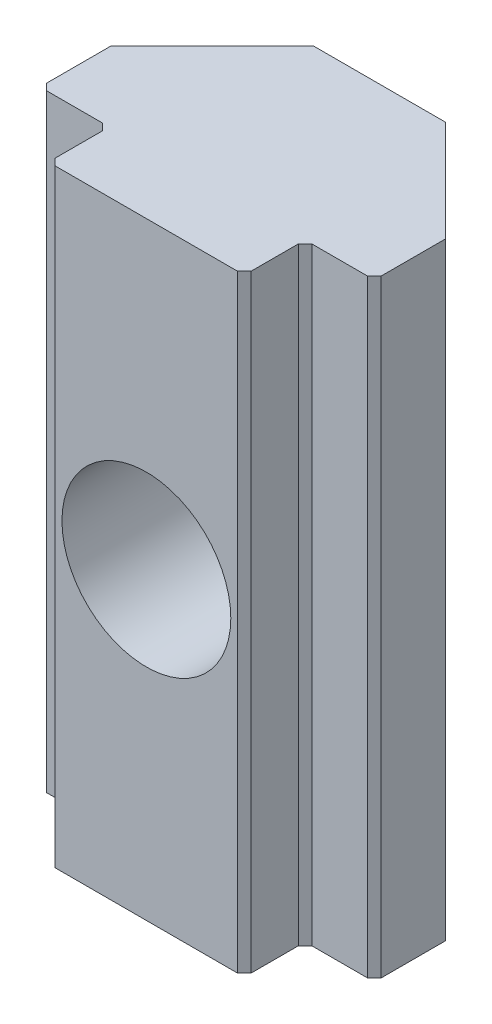
SolidWorks part; units mm, degrees
material "201 退火不锈钢 (SS)"
ref_plane "前视基准面" through (0, 0, 0) normal (0, 0, 1) x (1, 0, 0)
ref_plane "上视基准面" through (0, 0, 0) normal (0, 1, 0) x (1, 0, 0)
ref_plane "右视基准面" through (0, 0, 0) normal (1, 0, 0) x (0, 0, -1)
sketch "草图1" plane through (0, 0, 0) normal (0, 1, 0) x (1, 0, 0)
  line L0 (2.9, -2.55) -> (4.95, -2.55)
  line L1 (-4.95, -2.55) -> (-2.9, -2.55)
  line L2 (-4.95, -2.55) -> (-4.95, 2.55)
  line L3 (-4.95, 2.55) -> (4.95, 2.55)
  line L4 (4.95, -2.55) -> (4.95, 2.55)
  line L5 (-4.95, -2.55) -> (4.95, 2.55) construction
  line L6 (-4.95, 2.55) -> (4.95, -2.55) construction
  line L7 (-2.9, -4.35) -> (2.9, -4.35)
  line L8 (-2.9, -4.35) -> (-2.9, -2.55)
  line L10 (2.9, -4.35) -> (2.9, -2.55)
  line L11 (-2.9, -4.35) -> (2.9, -2.55) construction
  line L12 (-2.9, -2.55) -> (2.9, -4.35) construction
  point P0 (0, 0)
  point P6 (0, -3.45)
  dimension "D1" = 5.8
  dimension "D2" = 1.8
  dimension "D3" = 6.9
  dimension "D4" = 9.9
  dimension "D5" = 0
extrude "凸台-拉伸1" add sketch "草图1" along normal blind 18
chamfer "倒角1" distance 3 angle 45 2 edges at (-4.95, 9, -2.55) (4.95, 9, -2.55)
chamfer "倒角2" distance 0.2 angle 45 6 edges at (-2.9, 9, 2.55) (-4.95, 9, 2.55) (4.95, 9, 2.55) (2.9, 9, 2.55) (2.9, 9, 4.35) (-2.9, 9, 4.35)
hole_wizard "M6 螺纹孔1" positions "草图2" profile "草图3" tap size "M6" standard "GB" end condition through all
sketch "草图2" plane through (0, 0, 4.35) normal (0, 0, 1) x (1, 0, 0)
  point P0 (0, 9)
sketch "草图3" plane through (0, 9, 4.35) normal (1, 0, 0) x (0, -1, 0)
  line L0 (0, 0) -> (0, 6.9)
  line L1 (0, 6.9) -> (2.5, 6.9)
  line L2 (2.5, 6.9) -> (2.5, 0)
  line L5 (2.5, 0) -> (0, 0)
  line L11 (0, -6.35) -> (0, 107.95) construction
  dimension "通孔螺纹孔钻头直径" = 5
  dimension "通孔螺纹孔钻头深度" = 6.9
cosmetic thread "孔螺蚊线1" parameters "D2"=6
